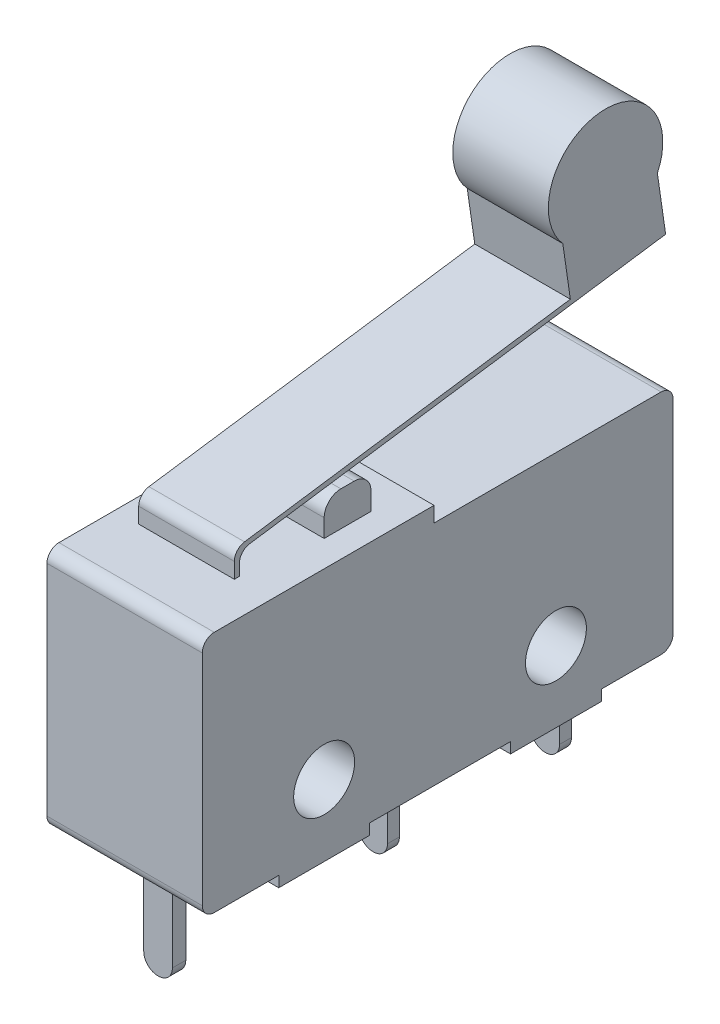
SolidWorks part; units mm, degrees
ref_plane "Front Plane" through (0, 0, 0) normal (0, 0, 1) x (1, 0, 0)
ref_plane "Top Plane" through (0, 0, 0) normal (0, 1, 0) x (1, 0, 0)
ref_plane "Right Plane" through (0, 0, 0) normal (1, 0, 0) x (0, 0, -1)
sketch "Sketch1" plane through (0, 0, 0) normal (1, 0, 0) x (0, 0, -1)
  line L0 (-37.3731, 0) -> (-34.6731, 0)
  line L1 (-37.8731, 0.5) -> (-37.8731, 9.66)
  line L2 (-37.3731, 10.16) -> (-28.1731, 10.16)
  line L3 (-28.1731, 10.16) -> (-28.1731, 9.52)
  line L4 (-28.1731, 9.52) -> (-18.6731, 9.52)
  line L5 (-18.1731, 9.02) -> (-18.1731, 0.5)
  line L6 (-34.6731, 0) -> (-34.6731, -0.45)
  line L7 (-34.6731, -0.45) -> (-30.8731, -0.45)
  line L8 (-30.8731, -0.45) -> (-30.8731, 0)
  line L9 (-30.8731, 0) -> (-24.9731, 0)
  line L10 (-24.9731, 0) -> (-24.9731, -0.45)
  line L11 (-24.9731, -0.45) -> (-21.1731, -0.45)
  line L12 (-21.1731, -0.45) -> (-21.1731, 0)
  line L13 (-21.1731, 0) -> (-18.6731, 0)
  line L14 (-32.7731, -0.45) -> (-32.7731, 2.9938) construction
  line L15 (-23.0731, -0.45) -> (-23.0731, 2.9938) construction
  arc A0 (-18.6731, 9.52) -> (-18.1731, 9.02) centre (-18.6731, 9.02) cw
  arc A1 (-18.6731, 0) -> (-18.1731, 0.5) centre (-18.6731, 0.5) ccw
  arc A2 (-37.3731, 0) -> (-37.8731, 0.5) centre (-37.3731, 0.5) cw
  arc A3 (-37.8731, 9.66) -> (-37.3731, 10.16) centre (-37.3731, 9.66) cw
  circle A4 centre (-32.7731, 2.525) radius 1.275
  circle A5 centre (-23.0731, 2.525) radius 1.275
  point P18 (-23.0731, -0.45)
  point P19 (-18.1731, 9.52)
  point P22 (-18.1731, 0)
  point P25 (-37.8731, 0)
  point P28 (-37.8731, 10.16)
  point P29 (-32.7731, -0.45)
  point P38 (-32.7731, 1.25)
  point P39 (-23.0731, 1.25)
  dimension "D11" = 0.5
  dimension "D12" = 2.55
  dimension "D13" = 2.55
  dimension "D1" = 9.52
  dimension "D2" = 10.16
  dimension "D3" = 3.8
  dimension "D4" = 3.8
  dimension "D5" = 0.45
  dimension "D6" = 0.45
  dimension "D7" = 19.7
  dimension "D8" = 3.2
  dimension "D9" = 9.7
  dimension "D10" = 5.9
  dimension "D14" = 1.7
  dimension "D15" = 1.7
extrude "Boss-Extrude1" add sketch "Sketch1" along normal blind 6.5
sketch "Sketch2" plane through (0, 10.16, 0) normal (0, 1, 0) x (1, 0, 0)
  line L0 (6.5, -28.1731) -> (6.5, -37.3731) construction
  line L1 (5.4, -31.6731) -> (1.87, -31.6731)
  line L2 (5.4, -31.6731) -> (5.4, -29.7131)
  line L3 (5.4, -29.7131) -> (1.87, -29.7131)
  line L4 (1.87, -31.6731) -> (1.87, -29.7131)
  line L5 (5.4, -31.6731) -> (1.87, -29.7131) construction
  line L6 (5.4, -29.7131) -> (1.87, -31.6731) construction
  line L7 (6.5, -37.8731) -> (0, -37.8731) construction
  point P0 (3.635, -30.6931)
  dimension "D1" = 1.96
  dimension "D2" = 3.53
  dimension "D3" = 1.1
  dimension "D4" = 6.2
extrude "Boss-Extrude2" add sketch "Sketch2" along normal blind 1.45
fillet "Fillet1" radius 0.7 2 edges at (3.635, 11.61, 29.7131) (3.635, 11.61, 31.6731)
sketch "Sketch3" plane through (0, 0, 0) normal (0, -1, 0) x (-1, 0, 0)
  line L0 (-3.25, -37.3731) -> (-3.25, -18.1731) construction
  line L1 (-6.5, -37.3731) -> (0, -37.3731) construction
  line L2 (-6.5, -18.1731) -> (0, -18.1731) construction
  line L3 (-6.5, -37.8731) -> (0, -37.8731) construction
  line L4 (-1.65, -36.4731) -> (-4.85, -36.4731)
  line L5 (-1.65, -36.4731) -> (-1.65, -35.9131)
  line L6 (-1.65, -35.9131) -> (-4.85, -35.9131)
  line L7 (-4.85, -36.4731) -> (-4.85, -35.9131)
  line L8 (-1.65, -36.4731) -> (-4.85, -35.9131) construction
  line L9 (-1.65, -35.9131) -> (-4.85, -36.4731) construction
  line L10 (-1.65, -26.9731) -> (-4.85, -26.9731)
  line L11 (-1.65, -26.9731) -> (-1.65, -27.4731)
  line L12 (-1.65, -27.4731) -> (-4.85, -27.4731)
  line L13 (-4.85, -26.9731) -> (-4.85, -27.4731)
  line L14 (-1.65, -26.9731) -> (-4.85, -27.4731) construction
  line L15 (-1.65, -27.4731) -> (-4.85, -26.9731) construction
  line L16 (-1.65, -19.7731) -> (-4.85, -19.7731)
  line L17 (-1.65, -19.7731) -> (-1.65, -20.2731)
  line L18 (-1.65, -20.2731) -> (-4.85, -20.2731)
  line L19 (-4.85, -19.7731) -> (-4.85, -20.2731)
  line L20 (-1.65, -19.7731) -> (-4.85, -20.2731) construction
  line L21 (-1.65, -20.2731) -> (-4.85, -19.7731) construction
  point P6 (-3.25, -36.1931)
  point P11 (-3.25, -27.2231)
  point P16 (-3.25, -20.0231)
  dimension "D1" = 3.2
  dimension "D2" = 0.56
  dimension "D3" = 3.2
  dimension "D4" = 0.5
  dimension "D5" = 3.2
  dimension "D6" = 0.5
  dimension "D7" = 1.6
  dimension "D8" = 1.4
  dimension "D9" = 6.7
extrude "Boss-Extrude3" add sketch "Sketch3" along normal blind 0.9
sketch "Sketch4" plane through (0, -0.9, 0) normal (0, -1, 0) x (-1, 0, 0)
  line L0 (-3.25, -36.4731) -> (-3.25, -19.7731) construction
  line L1 (-4.85, -36.4731) -> (-1.65, -36.4731) construction
  line L2 (-1.65, -19.7731) -> (-4.85, -19.7731) construction
  line L3 (-4.85, -36.4731) -> (-1.65, -36.4731) construction
  line L4 (-2.65, -36.4731) -> (-3.85, -36.4731)
  line L5 (-2.65, -36.4731) -> (-2.65, -35.9131)
  line L6 (-2.65, -35.9131) -> (-3.85, -35.9131)
  line L7 (-3.85, -36.4731) -> (-3.85, -35.9131)
  line L8 (-2.65, -36.4731) -> (-3.85, -35.9131) construction
  line L9 (-2.65, -35.9131) -> (-3.85, -36.4731) construction
  line L10 (-1.65, -35.9131) -> (-4.85, -35.9131) construction
  line L11 (-4.85, -27.4731) -> (-1.65, -27.4731) construction
  line L12 (-3.85, -26.9731) -> (-2.65, -26.9731)
  line L13 (-3.85, -26.9731) -> (-3.85, -27.4731)
  line L14 (-3.85, -27.4731) -> (-2.65, -27.4731)
  line L15 (-2.65, -26.9731) -> (-2.65, -27.4731)
  line L16 (-3.85, -26.9731) -> (-2.65, -27.4731) construction
  line L17 (-3.85, -27.4731) -> (-2.65, -26.9731) construction
  line L18 (-1.65, -26.9731) -> (-4.85, -26.9731) construction
  line L19 (-4.85, -20.2731) -> (-1.65, -20.2731) construction
  line L20 (-3.85, -19.7731) -> (-2.65, -19.7731)
  line L21 (-3.85, -19.7731) -> (-3.85, -20.2731)
  line L22 (-3.85, -20.2731) -> (-2.65, -20.2731)
  line L23 (-2.65, -19.7731) -> (-2.65, -20.2731)
  line L24 (-3.85, -19.7731) -> (-2.65, -20.2731) construction
  line L25 (-3.85, -20.2731) -> (-2.65, -19.7731) construction
  line L26 (-1.65, -19.7731) -> (-4.85, -19.7731) construction
  point P6 (-3.25, -36.1931)
  point P15 (-3.25, -27.2231)
  point P24 (-3.25, -20.0231)
  dimension "D1" = 1.2
  dimension "D2" = 1.2
  dimension "D3" = 1.2
extrude "Boss-Extrude4" add sketch "Sketch4" along normal blind 3.47
fillet "Fillet2" radius 0.59 6 edges at (2.65, -4.37, 36.1931) (3.85, -4.37, 36.1931) (2.65, -4.37, 27.2231) (3.85, -4.37, 27.2231) (3.85, -4.37, 20.0231) (2.65, -4.37, 20.0231)
sketch "Эскиз1" plane through (6.5, 0, 0) normal (1, 0, 0) x (0, 0, -1)
  line L0 (-34.8206, 10.16) -> (-34.8206, 11.0655)
  line L1 (-34.8206, 11.0655) -> (-16.9831, 13.64)
  line L2 (-16.9831, 13.64) -> (-17.5158, 17.3307)
  line L3 (-21.4746, 16.7581) -> (-20.9705, 13.2798)
  line L4 (-20.9705, 13.2798) -> (-35.0331, 11.2417)
  line L5 (-35.0331, 11.2417) -> (-35.0331, 10.16)
  line L6 (-28.1731, 10.16) -> (-37.3731, 10.16) construction
  line L7 (-35.0331, 10.16) -> (-34.8206, 10.16)
  line L8 (-37.8731, 9.66) -> (-37.8731, 0.5) construction
  line L9 (-18.1731, 0.5) -> (-18.1731, 9.02) construction
  line L10 (-19.4953, 19.44) -> (-23.4649, 19.44)
  arc A0 (-17.5158, 17.3307) -> (-21.4746, 16.7581) centre (-19.4953, 17.045) ccw
  circle A1 centre (-19.4953, 17.045) radius 2.395
  line M5 (-28.1731, 10.16) -> (-37.3731, 10.16)
  dimension "D1" = 2.84
  dimension "D2" = 4.79
  dimension "D3" = 2
  dimension "D4" = 1.19
extrude "Бобышка-Вытянуть1" add sketch "Эскиз1" against normal blind 4 from offset 1.5 contours A1 L3 L4 L5 L0 L1 L2 M5 | L3 A1 L2 A0 | A1 L3 A0 L2 offset against normal yes
fillet "Скругление1" radius 0.5 2 edges at (3, 11.0655, 34.8206) (3, 11.2417, 35.0331)
